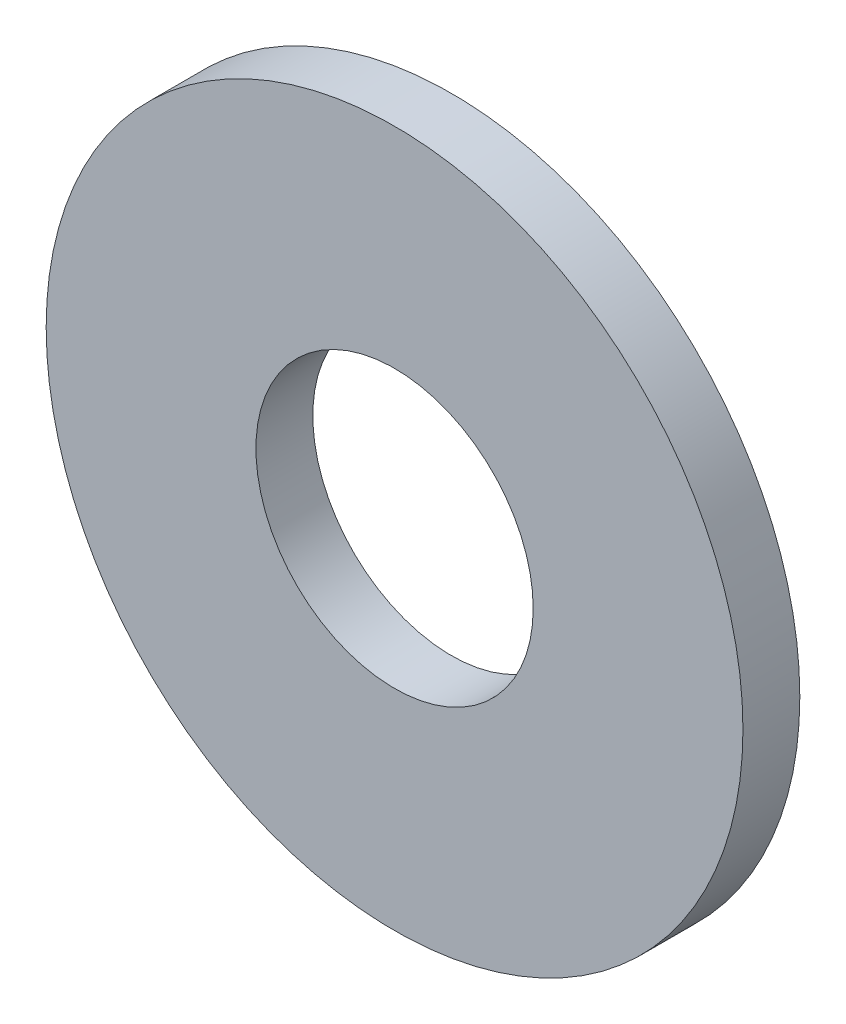
SolidWorks part; units mm, degrees
ref_plane "Front" through (0, 0, 0) normal (0, 0, 1) x (1, 0, 0)
ref_plane "Top" through (0, 0, 0) normal (0, 1, 0) x (1, 0, 0)
ref_plane "Right" through (0, 0, 0) normal (1, 0, 0) x (0, 0, -1)
sketch "Sketch1" plane through (0, 0, 0) normal (0, 0, 1) x (1, 0, 0)
  circle A0 centre (0, 0) radius 0.975
  circle A1 centre (0, 0) radius 2.45
  dimension "D1" = 1.95
  dimension "D2" = 4.9
extrude "Boss-Extrude1" add sketch "Sketch1" along normal blind 0.4
